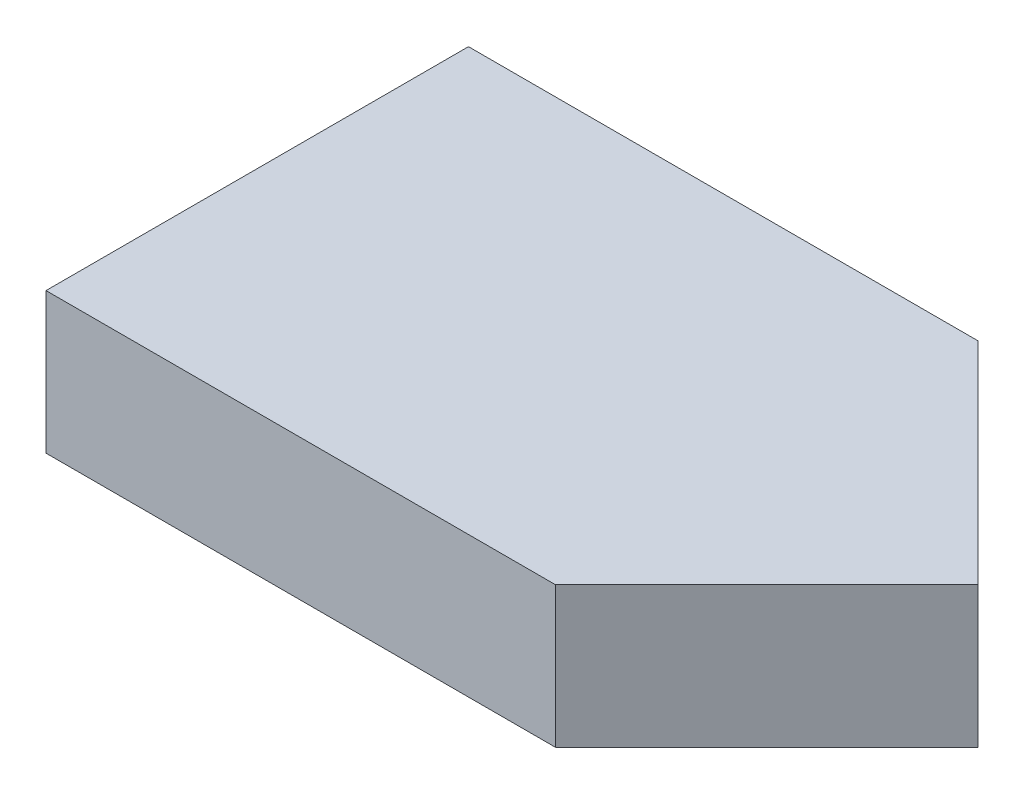
SolidWorks part; units mm, degrees
ref_plane "Front Plane" through (0, 0, 0) normal (0, 0, 1) x (1, 0, 0)
ref_plane "Top Plane" through (0, 0, 0) normal (0, 1, 0) x (1, 0, 0)
ref_plane "Right Plane" through (0, 0, 0) normal (1, 0, 0) x (0, 0, -1)
sketch "Sketch1" plane through (0, 0, 0) normal (0, 1, 0) x (1, 0, 0)
  line L0 (91.9, 76.2) -> (130, 38.1)
  line L1 (0, 0) -> (91.9, 0)
  line L2 (0, 0) -> (0, 76.2)
  line L3 (0, 76.2) -> (91.9, 76.2)
  line L4 (91.9, 0) -> (91.9, 76.2)
  line L5 (130, 38.1) -> (91.9, 0)
  line L6 (0, 38.1) -> (130, 38.1)
  dimension "D1" = 76.2
  dimension "D2" = 130
extrude "Boss-Extrude1" add sketch "Sketch1" along normal blind 25.4 contours L6 L2 L1 L4 | L6 L4 L5 | L4 L6 L0 | L2 L6 L4 L3
